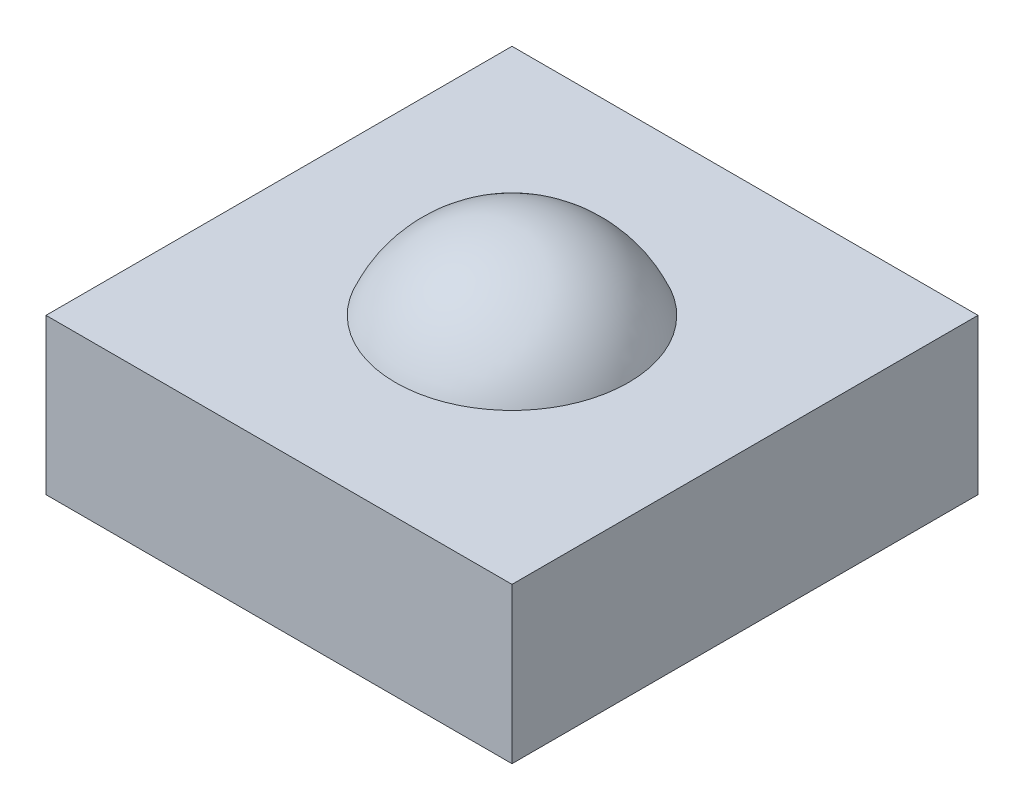
SolidWorks part; units mm, degrees
ref_plane "Front Plane" through (0, 0, 0) normal (0, 0, 1) x (1, 0, 0)
ref_plane "Top Plane" through (0, 0, 0) normal (0, 1, 0) x (1, 0, 0)
ref_plane "Right Plane" through (0, 0, 0) normal (1, 0, 0) x (0, 0, -1)
sketch "Sketch1" plane through (0, 0, 0) normal (0, 1, 0) x (1, 0, 0)
  line L1 (-0.3, 0.3) -> (0.3, 0.3)
  line L2 (-0.3, 0.3) -> (-0.3, -0.3)
  line L3 (-0.3, -0.3) -> (0.3, -0.3)
  line L4 (0.3, 0.3) -> (0.3, -0.3)
  line L5 (-0.3, 0.3) -> (0.3, -0.3) construction
  line L6 (-0.3, -0.3) -> (0.3, 0.3) construction
  point P0 (0, 0)
  dimension "D1" = 0.6
extrude "Boss-Extrude1" add sketch "Sketch1" along normal blind 0.2
sketch "Sketch2" plane through (0, 0, 0) normal (0, 0, 1) x (1, 0, 0)
  line L0 (-0.1963, 0.3) -> (0.3349, 0.3) construction
  line L2 (-0.3, 0.2) -> (0.3, 0.2) construction
  line L4 (0, 0.2) -> (0.15, 0.2)
  line L5 (0, 0.2) -> (0, 0.3)
  arc A0 (0.15, 0.2) -> (0, 0.3) centre (0, 0.1375) ccw
  dimension "D1" = 0.15
  dimension "D2" = 0.1
revolve "Revolve1" add sketch "Sketch2" angle 360 about L5
sketch "Orientation Sketch" plane through (0, 0.2, 0) normal (0, 1, 0) x (1, 0, 0)
  line L0 (0.3, -0.3) -> (0.3, 0.3) construction
  line L1 (0.3, 0.3) -> (-0.3, 0.3) construction
  line L2 (-0.3, 0.3) -> (-0.3, -0.3) construction
  line L3 (-0.3, -0.3) -> (0.3, -0.3) construction
  line L4 (0.3, -0.3) -> (0.3, 0.3) construction
  line L5 (0.3, 0.3) -> (-0.3, 0.3) construction
  line L6 (-0.3, 0.3) -> (-0.3, -0.3) construction
  line L7 (-0.3, -0.3) -> (0.3, -0.3) construction
  circle A0 centre (0, 0) radius 0.15 construction
  circle A1 centre (0, 0) radius 0.15
  point P7 (0, 0)
other "FormTool1"
